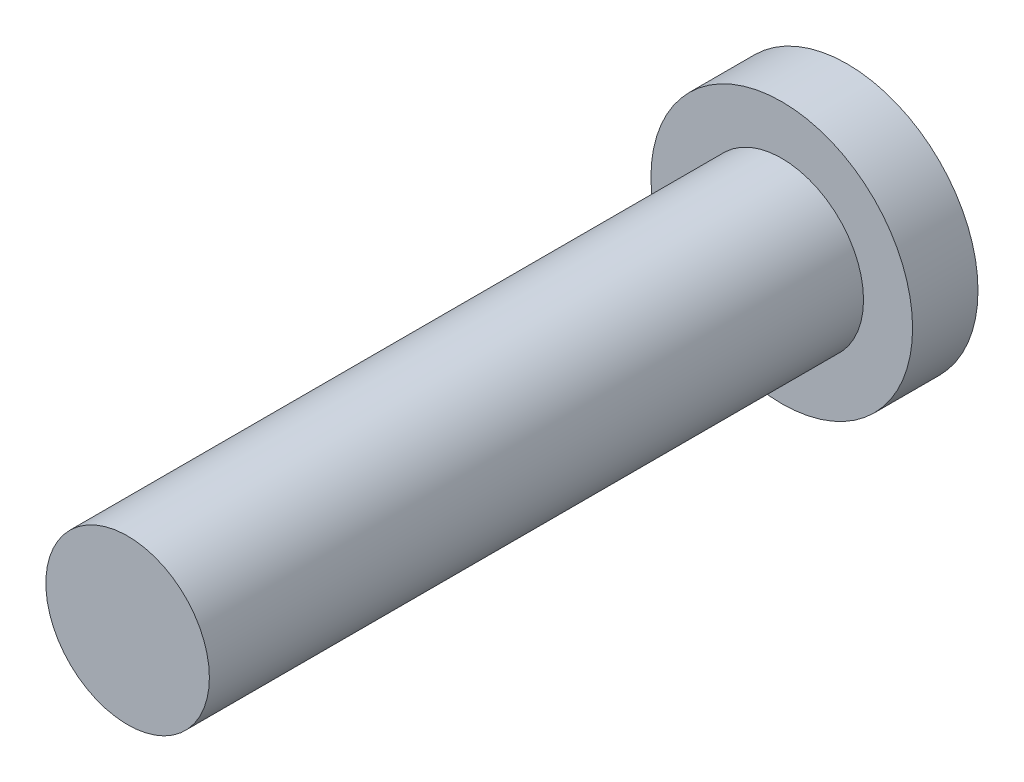
SolidWorks part; units mm, degrees
ref_plane "前视基准面" through (0, 0, 0) normal (0, 0, 1) x (1, 0, 0)
ref_plane "上视基准面" through (0, 0, 0) normal (0, 1, 0) x (1, 0, 0)
ref_plane "右视基准面" through (0, 0, 0) normal (1, 0, 0) x (0, 0, -1)
sketch "草图1" plane through (0, 0, 0) normal (0, 0, 1) x (1, 0, 0)
  circle A0 centre (0, 0) radius 4
  dimension "D1" = 8
extrude "凸台-拉伸1" add sketch "草图1" along normal blind 2
sketch "草图2" plane through (0, 0, 2) normal (0, 0, 1) x (1, 0, 0)
  circle A0 centre (0, 0) radius 2.5
  dimension "D1" = 5
extrude "凸台-拉伸2" add sketch "草图2" along normal blind 20
